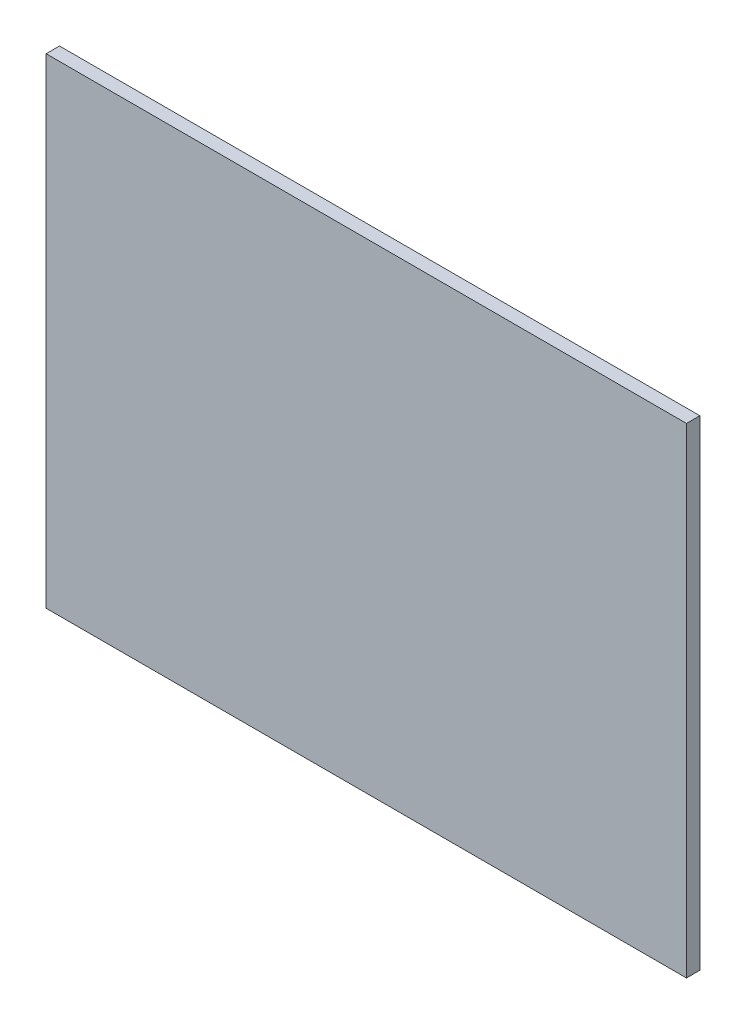
SolidWorks part; units mm, degrees
ref_plane "Front Plane" through (0, 0, 0) normal (0, 0, 1) x (1, 0, 0)
ref_plane "Top Plane" through (0, 0, 0) normal (0, 1, 0) x (1, 0, 0)
ref_plane "Right Plane" through (0, 0, 0) normal (1, 0, 0) x (0, 0, -1)
sketch "Sketch1" plane through (0, 0, 0) normal (0, 0, 1) x (1, 0, 0)
  line L1 (-76.2, 57.15) -> (76.2, 57.15)
  line L2 (-76.2, 57.15) -> (-76.2, -57.15)
  line L3 (-76.2, -57.15) -> (76.2, -57.15)
  line L4 (76.2, 57.15) -> (76.2, -57.15)
  line L5 (-76.2, 57.15) -> (76.2, -57.15) construction
  line L6 (-76.2, -57.15) -> (76.2, 57.15) construction
  point P0 (0, 0)
  dimension "D1" = 114.3
  dimension "D2" = 152.4
extrude "Boss-Extrude1" add sketch "Sketch1" along normal blind 3.18
